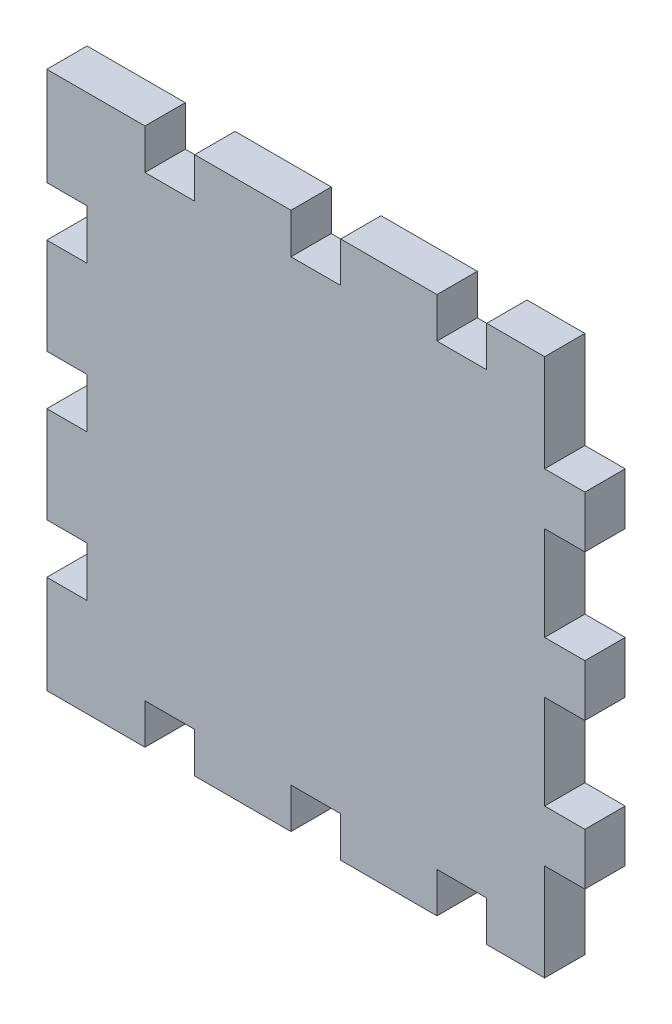
SolidWorks part; units mm, degrees
ref_plane "Front Plane" through (0, 0, 0) normal (0, 0, 1) x (1, 0, 0)
ref_plane "Top Plane" through (0, 0, 0) normal (0, 1, 0) x (1, 0, 0)
ref_plane "Right Plane" through (0, 0, 0) normal (1, 0, 0) x (0, 0, -1)
sketch "Sketch2" plane through (0, 0, 0) normal (0, 0, 1) x (1, 0, 0)
  line L1 (-2, 21.15) -> (-2, 17.975)
  line L2 (-13.5, 21.15) -> (-13.5, 17.975)
  line L3 (-13.5, 17.975) -> (-9.5, 17.975)
  line L4 (-9.5, 21.15) -> (-9.5, 17.975)
  line L5 (13.5, 21.15) -> (13.5, 17.975)
  line L6 (13.5, 17.975) -> (9.5, 17.975)
  line L9 (9.5, 21.15) -> (9.5, 17.975)
  line L10 (-2, 17.975) -> (2, 17.975)
  line L12 (-21.15, 21.15) -> (17.975, 21.15)
  line L13 (-21.15, 21.15) -> (-21.15, -21.15)
  line L14 (-21.15, -21.15) -> (17.975, -21.15)
  line L15 (21.15, 13.5) -> (21.15, 9.5)
  line L16 (-21.15, 21.15) -> (21.15, -21.15) construction
  line L17 (-21.15, -21.15) -> (21.15, 21.15) construction
  line L19 (17.975, 21.15) -> (17.975, 13.5)
  line L20 (21.15, 2) -> (21.15, -2)
  line L21 (21.15, -9.5) -> (21.15, -13.5)
  line L22 (17.975, 9.5) -> (17.975, 2)
  line L23 (17.975, -2) -> (17.975, -9.5)
  line L24 (17.975, -13.5) -> (17.975, -21.15)
  line L30 (2, 21.15) -> (2, 17.975)
  line L31 (-2, 21.15) -> (2, 17.975) construction
  line L32 (-2, 17.975) -> (2, 21.15) construction
  line L33 (-2, 21.15) -> (2, 21.15)
  line L34 (-2, -17.975) -> (-2, -21.15)
  line L35 (-13.5, -17.975) -> (-13.5, -21.15)
  line L36 (-13.5, -21.15) -> (-9.5, -21.15)
  line L37 (-9.5, -17.975) -> (-9.5, -21.15)
  line L38 (13.5, -17.975) -> (13.5, -21.15)
  line L39 (13.5, -21.15) -> (9.5, -21.15)
  line L40 (9.5, -17.975) -> (9.5, -21.15)
  line L41 (-2, -21.15) -> (2, -21.15)
  line L42 (2, -17.975) -> (2, -21.15)
  line L43 (-2, -17.975) -> (2, -21.15) construction
  line L44 (-2, -21.15) -> (2, -17.975) construction
  line L45 (-2, -17.975) -> (2, -17.975)
  line L46 (9.5, -17.975) -> (13.5, -17.975)
  line L47 (-13.5, -17.975) -> (-9.5, -17.975)
  line L49 (-21.15, -2) -> (-17.975, -2)
  line L50 (-21.15, -2) -> (-21.15, 2)
  line L51 (-21.15, 2) -> (-17.975, 2)
  line L52 (-17.975, -2) -> (-17.975, 2)
  line L54 (-21.15, 9.5) -> (-17.975, 9.5)
  line L55 (-21.15, 9.5) -> (-21.15, 13.5)
  line L56 (-21.15, 13.5) -> (-17.975, 13.5)
  line L57 (-17.975, 9.5) -> (-17.975, 13.5)
  line L58 (0, 21.15) -> (0, -21.15) construction
  line L59 (-21.15, -9.5) -> (-17.975, -9.5)
  line L60 (-21.15, -9.5) -> (-21.15, -13.5)
  line L61 (-21.15, -13.5) -> (-17.975, -13.5)
  line L62 (-17.975, -9.5) -> (-17.975, -13.5)
  line L64 (21.15, -13.5) -> (17.975, -13.5)
  line L65 (21.15, -9.5) -> (17.975, -9.5)
  line L67 (21.15, 13.5) -> (17.975, 13.5)
  line L68 (21.15, 9.5) -> (17.975, 9.5)
  line L70 (21.15, 2) -> (17.975, 2)
  line L71 (21.15, -2) -> (17.975, -2)
  point P0 (0, -21.15)
  point P9 (0, 19.5625)
  point P13 (0, 0)
  point P35 (0, 21.15)
  point P46 (0, -19.5625)
  point P62 (-17.975, 0)
  point P63 (-21.15, 0)
  dimension "D4" = 42.3
  dimension "D5" = 42.3
  dimension "D2" = 4
  dimension "D3" = 3.175
  dimension "D6" = 7.5
  dimension "D11" = 7.5
  dimension "D12" = 4
  dimension "D13" = 3.175
  dimension "D14" = 7.5
  dimension "D15" = 7.5
  dimension "D16" = 3.175
  dimension "D17" = 7.5
  dimension "D18" = 7.5
extrude "Boss-Extrude1" add sketch "Sketch2" along normal blind 3.175
sketch "Sketch3" plane through (0, 0, 3.175) normal (0, 0, 1) x (1, 0, 0)
  line L104 (18.0156, -2.0406) -> (21.1906, -2.0406)
  line L105 (21.1906, -2.0406) -> (21.1906, 2.0406)
  line L106 (21.1906, 2.0406) -> (18.0156, 2.0406)
  line L107 (18.0156, 2.0406) -> (18.0156, 9.4594)
  line L108 (18.0156, 9.4594) -> (21.1906, 9.4594)
  line L109 (21.1906, 9.4594) -> (21.1906, 13.5406)
  line L110 (21.1906, 13.5406) -> (18.0156, 13.5406)
  line L111 (18.0156, 13.5406) -> (18.0156, 21.1906)
  line L112 (18.0156, 21.1906) -> (13.4594, 21.1906)
  line L113 (13.4594, 21.1906) -> (13.4594, 18.0156)
  line L114 (13.4594, 18.0156) -> (9.5406, 18.0156)
  line L115 (9.5406, 18.0156) -> (9.5406, 21.1906)
  line L116 (9.5406, 21.1906) -> (1.9594, 21.1906)
  line L117 (1.9594, 21.1906) -> (1.9594, 18.0156)
  line L118 (1.9594, 18.0156) -> (-1.9594, 18.0156)
  line L119 (-1.9594, 18.0156) -> (-1.9594, 21.1906)
  line L120 (-1.9594, 21.1906) -> (-9.5406, 21.1906)
  line L121 (-9.5406, 21.1906) -> (-9.5406, 18.0156)
  line L122 (-9.5406, 18.0156) -> (-13.4594, 18.0156)
  line L123 (-13.4594, 18.0156) -> (-13.4594, 21.1906)
  line L124 (-13.4594, 21.1906) -> (-21.1906, 21.1906)
  line L125 (-21.1906, 21.1906) -> (-21.1906, 13.4594)
  line L126 (-21.1906, 13.4594) -> (-18.0156, 13.4594)
  line L127 (-18.0156, 13.4594) -> (-18.0156, 9.5406)
  line L128 (-18.0156, 9.5406) -> (-21.1906, 9.5406)
  line L129 (-21.1906, 9.5406) -> (-21.1906, 1.9594)
  line L130 (-21.1906, 1.9594) -> (-18.0156, 1.9594)
  line L131 (-18.0156, 1.9594) -> (-18.0156, -1.9594)
  line L132 (-18.0156, -1.9594) -> (-21.1906, -1.9594)
  line L133 (-21.1906, -1.9594) -> (-21.1906, -9.5406)
  line L134 (-21.1906, -9.5406) -> (-18.0156, -9.5406)
  line L135 (-18.0156, -9.5406) -> (-18.0156, -13.4594)
  line L136 (-18.0156, -13.4594) -> (-21.1906, -13.4594)
  line L137 (-21.1906, -13.4594) -> (-21.1906, -21.1906)
  line L138 (-21.1906, -21.1906) -> (-13.4594, -21.1906)
  line L139 (-13.4594, -21.1906) -> (-13.4594, -18.0156)
  line L140 (-13.4594, -18.0156) -> (-9.5406, -18.0156)
  line L141 (-9.5406, -18.0156) -> (-9.5406, -21.1906)
  line L142 (-9.5406, -21.1906) -> (-1.9594, -21.1906)
  line L143 (-1.9594, -21.1906) -> (-1.9594, -18.0156)
  line L144 (-1.9594, -18.0156) -> (1.9594, -18.0156)
  line L145 (1.9594, -18.0156) -> (1.9594, -21.1906)
  line L146 (1.9594, -21.1906) -> (9.5406, -21.1906)
  line L147 (9.5406, -21.1906) -> (9.5406, -18.0156)
  line L148 (9.5406, -18.0156) -> (13.4594, -18.0156)
  line L149 (13.4594, -18.0156) -> (13.4594, -21.1906)
  line L150 (13.4594, -21.1906) -> (18.0156, -21.1906)
  line L151 (18.0156, -21.1906) -> (18.0156, -13.5406)
  line L152 (18.0156, -13.5406) -> (21.1906, -13.5406)
  line L153 (21.1906, -13.5406) -> (21.1906, -9.4594)
  line L154 (21.1906, -9.4594) -> (18.0156, -9.4594)
  line L155 (18.0156, -9.4594) -> (18.0156, -2.0406)
  line L156 (18.0156, -2.0406) -> (21.1906, -2.0406)
  line L157 (21.1906, -2.0406) -> (21.1906, 2.0406)
  line L158 (21.1906, 2.0406) -> (18.0156, 2.0406)
  line L159 (18.0156, 2.0406) -> (18.0156, 9.4594)
  line L160 (18.0156, 9.4594) -> (21.1906, 9.4594)
  line L161 (21.1906, 9.4594) -> (21.1906, 13.5406)
  line L162 (21.1906, 13.5406) -> (18.0156, 13.5406)
  line L163 (18.0156, 13.5406) -> (18.0156, 21.1906)
  line L164 (18.0156, 21.1906) -> (13.4594, 21.1906)
  line L165 (13.4594, 21.1906) -> (13.4594, 18.0156)
  line L166 (13.4594, 18.0156) -> (9.5406, 18.0156)
  line L167 (9.5406, 18.0156) -> (9.5406, 21.1906)
  line L168 (9.5406, 21.1906) -> (1.9594, 21.1906)
  line L169 (1.9594, 21.1906) -> (1.9594, 18.0156)
  line L170 (1.9594, 18.0156) -> (-1.9594, 18.0156)
  line L171 (-1.9594, 18.0156) -> (-1.9594, 21.1906)
  line L172 (-1.9594, 21.1906) -> (-9.5406, 21.1906)
  line L173 (-9.5406, 21.1906) -> (-9.5406, 18.0156)
  line L174 (-9.5406, 18.0156) -> (-13.4594, 18.0156)
  line L175 (-13.4594, 18.0156) -> (-13.4594, 21.1906)
  line L176 (-13.4594, 21.1906) -> (-21.1906, 21.1906)
  line L177 (-21.1906, 21.1906) -> (-21.1906, 13.4594)
  line L178 (-21.1906, 13.4594) -> (-18.0156, 13.4594)
  line L179 (-18.0156, 13.4594) -> (-18.0156, 9.5406)
  line L180 (-18.0156, 9.5406) -> (-21.1906, 9.5406)
  line L181 (-21.1906, 9.5406) -> (-21.1906, 1.9594)
  line L182 (-21.1906, 1.9594) -> (-18.0156, 1.9594)
  line L183 (-18.0156, 1.9594) -> (-18.0156, -1.9594)
  line L184 (-18.0156, -1.9594) -> (-21.1906, -1.9594)
  line L185 (-21.1906, -1.9594) -> (-21.1906, -9.5406)
  line L186 (-21.1906, -9.5406) -> (-18.0156, -9.5406)
  line L187 (-18.0156, -9.5406) -> (-18.0156, -13.4594)
  line L188 (-18.0156, -13.4594) -> (-21.1906, -13.4594)
  line L189 (-21.1906, -13.4594) -> (-21.1906, -21.1906)
  line L190 (-21.1906, -21.1906) -> (-13.4594, -21.1906)
  line L191 (-13.4594, -21.1906) -> (-13.4594, -18.0156)
  line L192 (-13.4594, -18.0156) -> (-9.5406, -18.0156)
  line L193 (-9.5406, -18.0156) -> (-9.5406, -21.1906)
  line L194 (-9.5406, -21.1906) -> (-1.9594, -21.1906)
  line L195 (-1.9594, -21.1906) -> (-1.9594, -18.0156)
  line L196 (-1.9594, -18.0156) -> (1.9594, -18.0156)
  line L197 (1.9594, -18.0156) -> (1.9594, -21.1906)
  line L198 (1.9594, -21.1906) -> (9.5406, -21.1906)
  line L199 (9.5406, -21.1906) -> (9.5406, -18.0156)
  line L200 (9.5406, -18.0156) -> (13.4594, -18.0156)
  line L201 (13.4594, -18.0156) -> (13.4594, -21.1906)
  line L202 (13.4594, -21.1906) -> (18.0156, -21.1906)
  line L203 (18.0156, -21.1906) -> (18.0156, -13.5406)
  line L204 (18.0156, -13.5406) -> (21.1906, -13.5406)
  line L205 (21.1906, -13.5406) -> (21.1906, -9.4594)
  line L206 (21.1906, -9.4594) -> (18.0156, -9.4594)
  line L207 (18.0156, -9.4594) -> (18.0156, -2.0406)
  dimension "D1" = 0.0406
extrude "Boss-Extrude2" add sketch "Sketch3" against normal blind 3.175
equation "\"stepper width\"=4.23"
equation "\"stepper hole disctance\" = 3.1"
equation "\"stepper hole diameter\"=0.34"
equation "\"stepper shaft hole\"=2.4"
equation "\"tooth width\"=0.4"
equation "\"tooth thickness\"=0.3175"
equation "\"tooth to side\"=0.75"
equation "\"motor chamber height\" = 6"
equation "\"D4@Sketch2\"=\"stepper width\""
equation "\"D5@Sketch2\"=\"stepper width\""
equation "\"D16@Sketch2\"=\"tooth thickness\""
equation "\"D17@Sketch2\"=\"tooth to side\""
equation "\"D18@Sketch2\"=\"tooth to side\""
